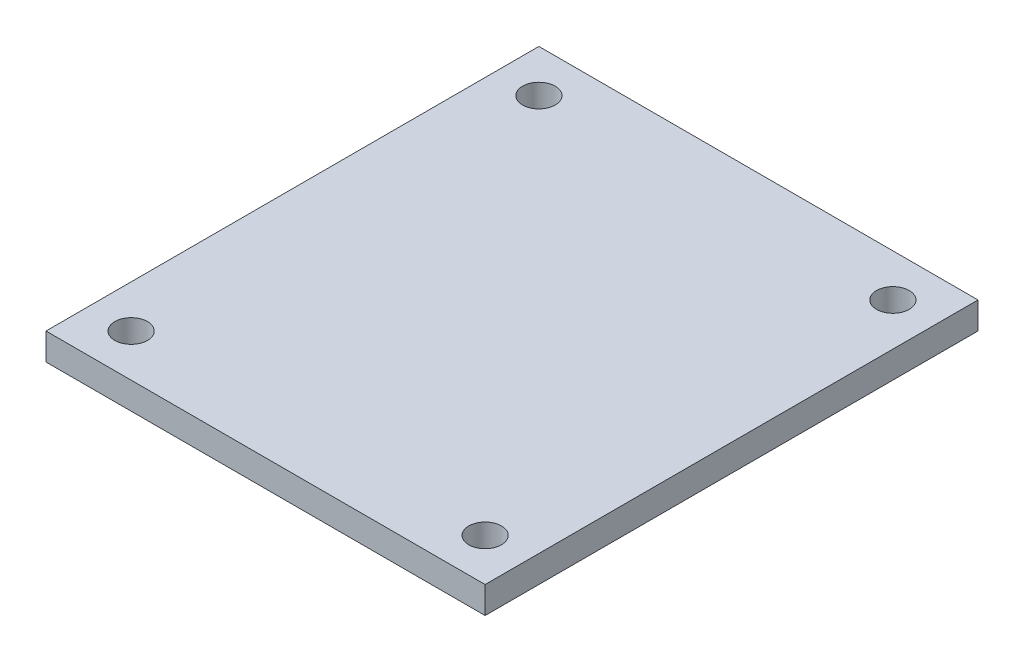
SolidWorks part; units mm, degrees
ref_plane "Plan de face" through (0, 0, 0) normal (0, 0, 1) x (1, 0, 0)
ref_plane "Plan de dessus" through (0, 0, 0) normal (0, 1, 0) x (1, 0, 0)
ref_plane "Plan de droite" through (0, 0, 0) normal (1, 0, 0) x (0, 0, -1)
sketch "Esquisse1" plane through (0, 0, 0) normal (0, 1, 0) x (1, 0, 0)
  line L1 (0, 0) -> (98, 0)
  line L2 (0, 0) -> (0, 110)
  line L3 (0, 110) -> (98, 110)
  line L4 (98, 0) -> (98, 110)
  dimension "D1" = 98
  dimension "D2" = 110
extrude "Boss.-Extru.1" add sketch "Esquisse1" along normal blind 6
sketch "Esquisse2" plane through (0, 6, 0) normal (0, 1, 0) x (1, 0, 0)
  line L0 (0, 110) -> (0, 0) construction
  line L1 (49, 110) -> (49, 0) construction
  line L2 (98, 110) -> (0, 110) construction
  line L3 (0, 0) -> (98, 0) construction
  line L4 (0, 55) -> (98, 55) construction
  line L5 (98, 0) -> (98, 110) construction
  circle A0 centre (9.5, 100.5) radius 3.65
  circle A1 centre (88.5, 100.5) radius 3.65
  circle A2 centre (88.5, 9.5) radius 3.65
  circle A3 centre (9.5, 9.5) radius 3.65
  dimension "D2" = 7.3
  dimension "D3" = 7.3
  dimension "D4" = 9.5
  dimension "D5" = 9.5
  dimension "D1" = 79
extrude "Enlèv. mat.-Extru.1" cut sketch "Esquisse2" against normal through all
